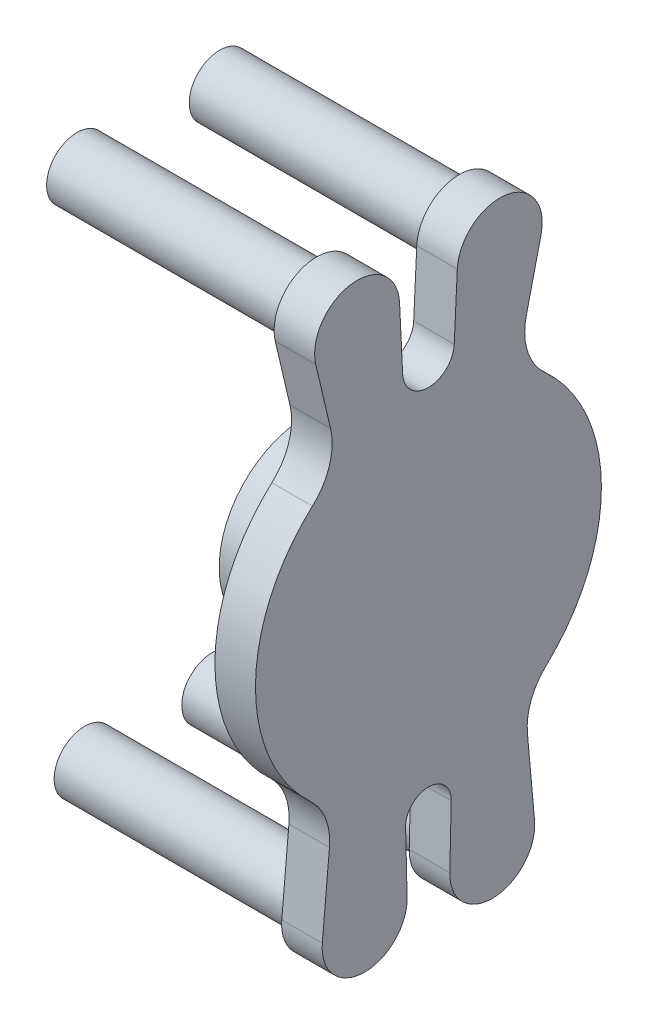
SolidWorks part; units mm, degrees
ref_plane "Front Plane" through (0, 0, 0) normal (0, 0, 1) x (1, 0, 0)
ref_plane "Top Plane" through (0, 0, 0) normal (0, 1, 0) x (1, 0, 0)
ref_plane "Right Plane" through (0, 0, 0) normal (1, 0, 0) x (0, 0, -1)
sketch "Sketch1" plane through (0, 0, 0) normal (0, 0, 1) x (1, 0, 0)
  line L0 (8.255, 0) -> (-8.255, 0) construction
  line L1 (25.4, 0) -> (-25.4, 0) construction
  line L2 (8.255, 0) -> (8.255, 18.542)
  line L3 (8.255, 18.542) -> (25.4, 18.542)
  line L4 (25.4, 18.542) -> (25.4, 0)
  line L5 (8.255, 0) -> (25.4, 0)
  point P4 (0, 0)
  point P8 (0, 0)
  dimension "D1" = 16.51
  dimension "D2" = 50.8
  dimension "D3" = 18.542
revolve "Revolve1" add sketch "Sketch1" angle 360 about L5
sketch "Sketch2" plane through (8.255, 0, 0) normal (-1, 0, 0) x (0, 0, 1)
  circle A0 centre (0, 0) radius 3.7147
  dimension "D1" = 7.4295
extrude "Cut-Extrude1" cut sketch "Sketch2" against normal blind 8.5725
sketch "Sketch3" plane through (25.4, 0, 0) normal (1, 0, 0) x (0, 0, -1)
  line L0 (0, 0) -> (0, -54.7688) construction
  line L1 (38.1, -54.7688) -> (-38.1, -54.7688) construction
  line L2 (38.1, -54.7688) -> (38.1, 54.7687) construction
  line L3 (38.1, 54.7687) -> (-38.1, 54.7687) construction
  line L4 (-38.1, -54.7688) -> (-38.1, 54.7687) construction
  line L5 (38.1, -54.7688) -> (-38.1, 54.7687) construction
  line L6 (38.1, 54.7687) -> (-38.1, -54.7688) construction
  line L7 (0, 0) -> (0, 54.7687) construction
  line L8 (-20.7029, 39.4483) -> (-23.827, 52.7082)
  line L9 (-6.1066, 55.2052) -> (-5.4533, 41.7705)
  line L10 (20.7029, 39.4483) -> (23.827, 52.7082)
  line L11 (6.1066, 55.2052) -> (5.4533, 41.7705)
  line L12 (38.1, 0) -> (-38.1, 0) construction
  line L13 (-20.9334, -37.1994) -> (-22.4428, -53.963)
  line L14 (-4.5111, -54.5527) -> (-4.8246, -41.518)
  line L15 (4.5111, -54.5527) -> (4.8246, -41.518)
  line L16 (20.9334, -37.1994) -> (22.4428, -53.963)
  circle A0 centre (15.0812, 54.7687) radius 6.4452 construction
  circle A1 centre (-15.0812, 54.7687) radius 6.4452 construction
  circle A2 centre (-13.4938, -54.7688) radius 6.4452 construction
  arc A4 (24.927, -26.7666) -> (24.5427, 27.1194) centre (0, 0) ccw
  arc A5 (-24.5427, 27.1194) -> (-20.7029, 39.4483) centre (-33.0644, 36.5358) ccw
  arc A6 (-6.1066, 55.2052) -> (-23.827, 52.7082) centre (-15.0812, 54.7687) ccw
  arc A7 (23.827, 52.7082) -> (6.1066, 55.2052) centre (15.0812, 54.7687) ccw
  arc A8 (-5.4533, 41.7705) -> (5.4533, 41.7705) centre (0, 42.0357) ccw
  arc A9 (24.5427, 27.1194) -> (20.7029, 39.4483) centre (33.0644, 36.5358) cw
  arc A10 (-22.4428, -53.963) -> (-4.5111, -54.5527) centre (-13.4938, -54.7688) ccw
  arc A11 (4.5111, -54.5527) -> (22.4428, -53.963) centre (13.4938, -54.7687) ccw
  arc A12 (-24.927, -26.7666) -> (-20.9334, -37.1994) centre (-33.5822, -36.0605) cw
  arc A13 (-4.8246, -41.518) -> (4.8246, -41.518) centre (0, -41.402) cw
  arc A14 (24.927, -26.7666) -> (20.9334, -37.1994) centre (33.5822, -36.0605) ccw
  circle A15 centre (-13.4938, -54.7688) radius 8.9852 construction
  arc A16 (-24.5427, 27.1194) -> (-24.927, -26.7666) centre (0, 0) ccw
  circle A17 centre (15.0812, 54.7687) radius 8.9852 construction
  circle A18 centre (-15.0812, 54.7687) radius 8.9852 construction
  point P0 (0, 0)
  point P6 (0, 0)
  point P39 (0, 0)
  dimension "D3" = 26.9875
  dimension "D5" = 9.0222
  dimension "D4" = 12.8905
  dimension "D7" = 73.152
  dimension "D9" = 12.7
  dimension "D12" = 5.4597
  dimension "D14" = 12.7
  dimension "D15" = 4.826
  dimension "D17" = 13.0347
  dimension "D1" = 109.5375
  dimension "D2" = 76.2
  dimension "D6" = 30.1625
  dimension "D10" = 13.2598
  dimension "D11" = 13.4347
  dimension "D16" = 16.7635
  dimension "D8" = 2.54
  dimension "D13" = 2.54
extrude "Boss-Extrude1" add sketch "Sketch3" along normal blind 8.5725
sketch "Sketch4" plane through (25.4, 0, 0) normal (-1, 0, 0) x (0, 0, 1)
  circle A0 centre (-15.0812, 54.7687) radius 6.4452 construction
  circle A1 centre (-15.0812, 54.7687) radius 6.4452
  circle A2 centre (15.0812, 54.7687) radius 6.4452 construction
  circle A3 centre (15.0812, 54.7687) radius 6.4452
  circle A4 centre (13.4938, -54.7688) radius 6.4452 construction
  circle A5 centre (13.4938, -54.7688) radius 6.4452
  circle A6 centre (-13.4938, -54.7687) radius 6.4452
  circle A7 centre (-15.0812, 54.7687) radius 4.7474
  circle A8 centre (15.0812, 54.7687) radius 4.7474
  circle A9 centre (-13.4938, -54.7687) radius 4.7474
  circle A10 centre (13.4938, -54.7688) radius 4.7474
  dimension "D1" = 12.8905
  dimension "D2" = 9.4949
extrude "Boss-Extrude2" add sketch "Sketch4" along normal blind 50.6451
